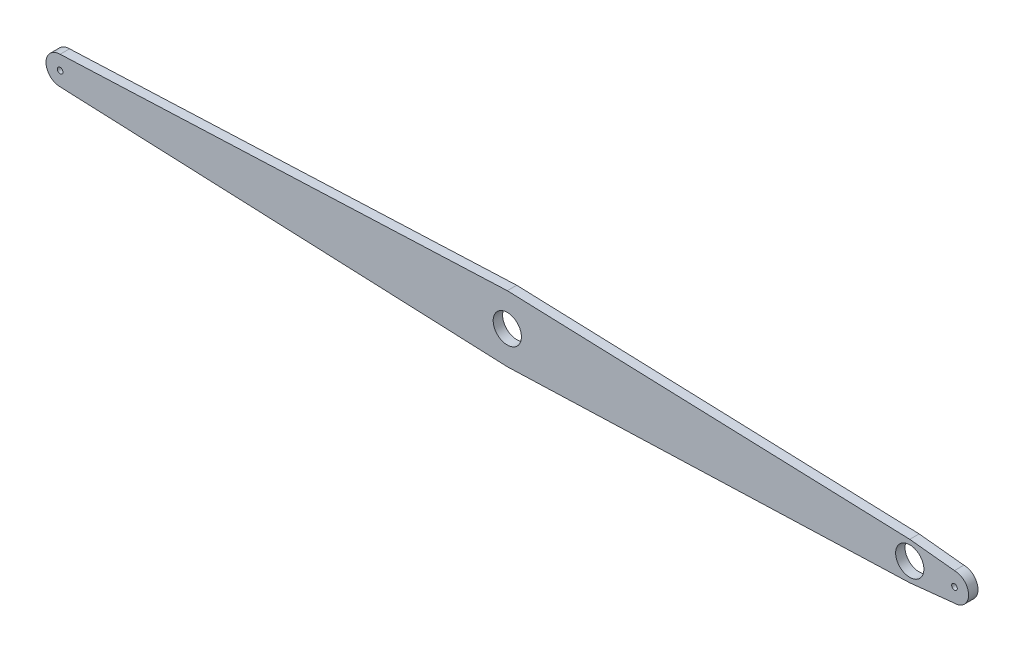
SolidWorks part; units mm, degrees
ref_plane "Ebene vorne" through (0, 0, 0) normal (0, 0, 1) x (1, 0, 0)
ref_plane "Ebene oben" through (0, 0, 0) normal (0, 1, 0) x (1, 0, 0)
ref_plane "Ebene rechts" through (0, 0, 0) normal (1, 0, 0) x (0, 0, -1)
sketch "Skizze1" plane through (0, 0, 0) normal (0, 0, 1) x (1, 0, 0)
  line L0 (0, 0) -> (-1900, 0) construction
  line L1 (-95, -40) -> (-95, 40) construction
  line L2 (-950, -70) -> (-950, 70) construction
  line L3 (0, 0) -> (81.758, 0) construction
  line L4 (-950, 70) -> (-95, 40)
  line L5 (-95, 40) -> (0, 30)
  line L6 (-1900, 0) -> (-1981.758, 0) construction
  line L7 (-1900, 30) -> (-950, 70)
  line L8 (-1900, -30) -> (-950, -70)
  line L9 (-95, -40) -> (0, -30)
  line L13 (-950, -70) -> (-95, -40)
  circle A0 centre (-950, 0) radius 30
  arc A1 (0, -30) -> (0, 30) centre (0, 0) ccw
  arc A2 (-1900, -30) -> (-1900, 30) centre (-1900, 0) cw
  circle A3 centre (-95, 0) radius 30
  circle A4 centre (-1900, 0) radius 6
  circle A5 centre (0, 0) radius 6
  point P3 (-95, 0)
  point P21 (-95, 0)
  dimension "D2" = 855
  dimension "D3" = 80
  dimension "D4" = 140
  dimension "D5" = 30
  dimension "D6" = 30
  dimension "D7" = 60
  dimension "D8" = 30
  dimension "D10" = 12
  dimension "D11" = 12
  dimension "D1" = 1900
  dimension "D9" = 60
extrude "Aufsatz-Linear austragen1" add sketch "Skizze1" along normal blind 20
